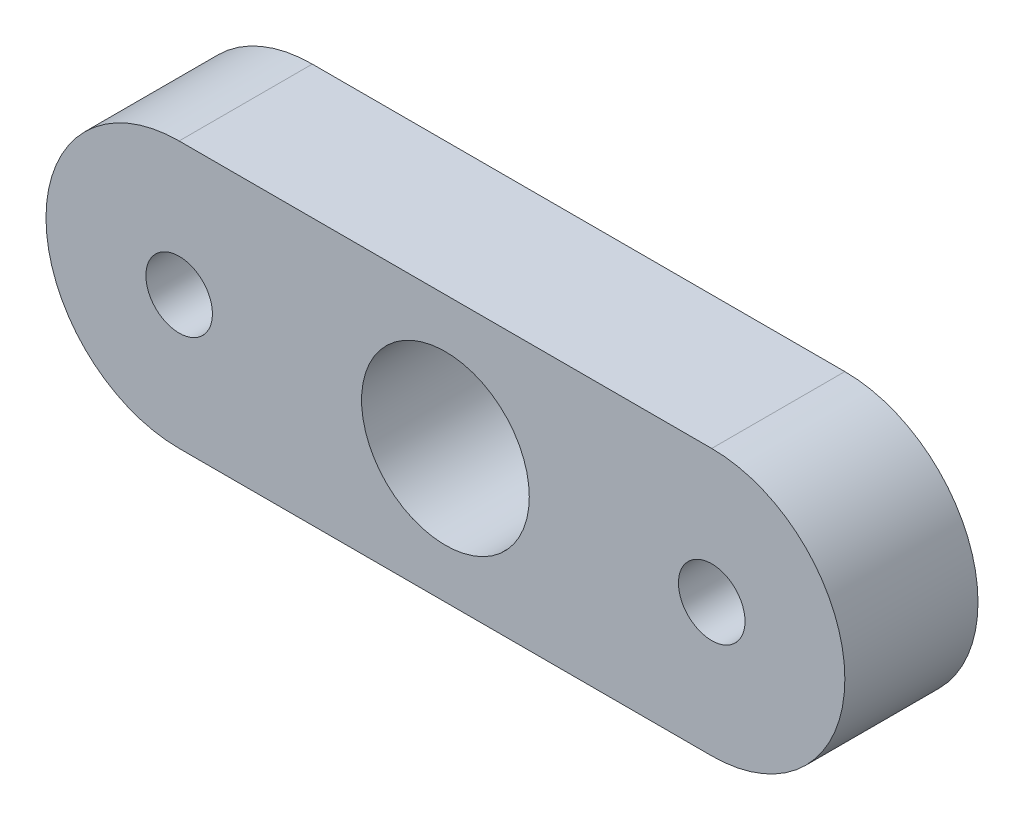
SolidWorks part; units mm, degrees
ref_plane "Front Plane" through (0, 0, 0) normal (0, 0, 1) x (1, 0, 0)
ref_plane "Top Plane" through (0, 0, 0) normal (0, 1, 0) x (1, 0, 0)
ref_plane "Right Plane" through (0, 0, 0) normal (1, 0, 0) x (0, 0, -1)
sketch "Sketch2" plane through (0, 0, 0) normal (0, 0, 1) x (1, 0, 0)
  line L0 (-6.35, 0) -> (6.35, 0) construction
  line L1 (-6.35, 3.175) -> (6.35, 3.175)
  line L2 (-6.35, -3.175) -> (6.35, -3.175)
  arc A0 (-6.35, 3.175) -> (-6.35, -3.175) centre (-6.35, 0) ccw
  arc A1 (6.35, -3.175) -> (6.35, 3.175) centre (6.35, 0) ccw
  circle A2 centre (0, 0) radius 2
  circle A5 centre (-6.35, 0) radius 0.7938
  circle A6 centre (6.35, 0) radius 0.7938
  point P2 (0, 0)
  dimension "D3" = 4
  dimension "D4" = 1.5875
  dimension "D5" = 1.5875
  dimension "D1" = 6.35
  dimension "D2" = 6.35
  dimension "D6" = 6.35
  dimension "D7" = 6.35
extrude "Boss-Extrude1" add sketch "Sketch2" along normal blind 3.175
